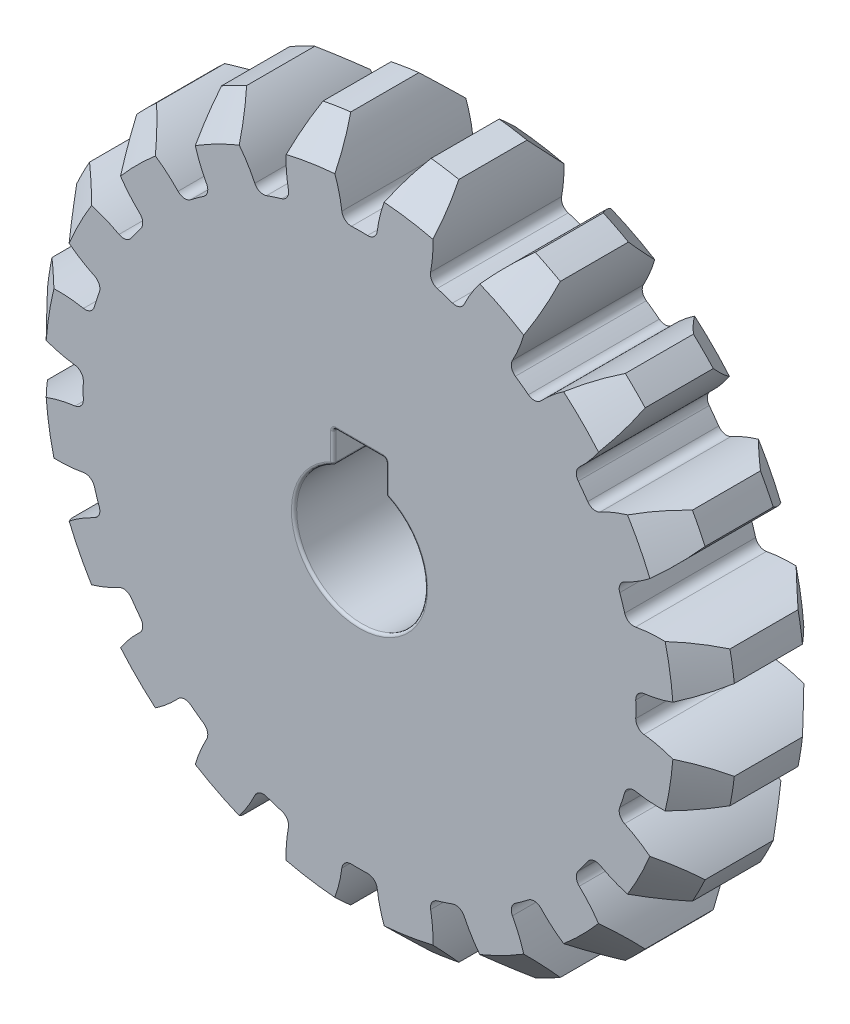
SolidWorks part; units mm, degrees
ref_plane "Front Plane" through (0, 0, 0) normal (0, 0, 1) x (1, 0, 0)
ref_plane "Top Plane" through (0, 0, 0) normal (0, 1, 0) x (1, 0, 0)
ref_plane "Right Plane" through (0, 0, 0) normal (1, 0, 0) x (0, 0, -1)
sketch "Sketch1" plane through (0, 0, 0) normal (0, 0, 1) x (1, 0, 0)
  circle A0 centre (0, 0) radius 24 construction
  circle A1 centre (0, 0) radius 26.4
  dimension "D1" = 48
  dimension "D2" = 52.8
extrude "Boss-Extrude1" add sketch "Sketch1" along normal mid plane 10
sketch "Sketch2" plane through (0, 0, 0) normal (0, 0, 1) x (1, 0, 0)
  line L0 (0, 0) -> (0, 26.4) construction
  line L1 (0, 0) -> (8.158, 25.1079) construction
  line L2 (0, 0) -> (4.1299, 26.075) construction
  line L3 (-1.2871, 21.0607) -> (0, 0) construction
  line L4 (-1.883, 23.926) -> (1.883, 23.926) construction
  line L5 (1.883, 23.926) -> (5.6027, 23.3369) construction
  line L6 (-2.7319, 26.2583) -> (0, 18.7525) construction
  circle A0 centre (0, 0) radius 21.6 construction
  circle A2 centre (0, 0) radius 26.4 construction
  arc A3 (-3.0665, 26.2213) -> (-1.2871, 21.0607) centre (-11.4642, 20.4387) cw
  circle A4 centre (0, 0) radius 26.4 construction
  arc A5 (3.0665, 26.2213) -> (1.2871, 21.0607) centre (11.4642, 20.4387) ccw
  circle A6 centre (0, 0) radius 24 construction
  arc A7 (1.2871, 21.0607) -> (-1.2871, 21.0607) centre (0, 0) ccw
  arc A8 (3.0665, 26.2213) -> (-3.0665, 26.2213) centre (0, 0) ccw
  dimension "D1" = 18
  dimension "D2" = 4.8
  dimension "D4" = 20
  dimension "D3" = 0.5
extrude "Cut-Extrude1" cut sketch "Sketch2" against normal through all both and the other way through all contours A5 A8 A3 A7
fillet "Fillet1" radius 0.72 2 edges at (1.2871, 21.0607, 0) (-1.2871, 21.0607, 0)
chamfer "Chamfer1" distance 2.4 angle 45 2 edges at (0, -26.4, -5) (0, -26.4, 5)
pattern_circular "CirPattern1" count 20 over 360 about axis through (0, 0, 0) along (0, 0, 1) of "Fillet1", "Cut-Extrude1"
sketch "Sketch3" plane through (0, 0, 5) normal (0, 0, 1) x (1, 0, 0)
  line L2 (-2, 4.5826) -> (-2, 7)
  line L3 (-2, 7) -> (2, 7)
  line L4 (2, 4.5826) -> (2, 7)
  arc A0 (-2, 4.5826) -> (2, 4.5826) centre (0, 0) ccw
  point P3 (0, 5)
  point P5 (0, 7)
  dimension "D1" = 10
  dimension "D2" = 2
  dimension "D3" = 4
extrude "Cut-Extrude2" cut sketch "Sketch3" against normal through all
fillet "Fillet2" radius 0.2 12 edges at (0, -5, 5) (0, -5, -5) (-2, 4.5826, 0) (2, 4.5826, 0) (0, 7, -5) (0, 7, 5) (-2, 7, 0) (-2, 5.7913, -5) (-2, 5.7913, 5) (2, 5.7913, -5) (2, 7, 0) (2, 5.7913, 5)
sketch "Sketch5" plane through (0, 0, 0) normal (0, 0, 1) x (1, 0, 0)
  circle A0 centre (0, 0) radius 24
equation "\"Module\"= 2.4"
equation "\"Number of Teeth\"= 20'Number of Teeth"
equation "\"Pressure Angle\"= 20"
equation "\"D1@Sketch1\"=\"Module\" * \"Number of Teeth\""
equation "\"D2@Sketch1\"=( \"Number of Teeth\" + 2) * \"Module\""
equation "\"D1@Sketch2\"=360 / \"Number of Teeth\""
equation "\"D2@Sketch2\"= \"Module\" * 2"
equation "\"D4@Sketch2\"=\"Pressure Angle\""
equation "\"D1@Fillet1\"=0.3 * \"Module\""
equation "\"D1@CirPattern1\"= \"Number of Teeth\""
equation "\"D1@Chamfer1\"= \"Module\""
equation "\"Gear Thickness\"= 10"
equation "\"D1@Boss-Extrude1\"= \"Gear Thickness\""
